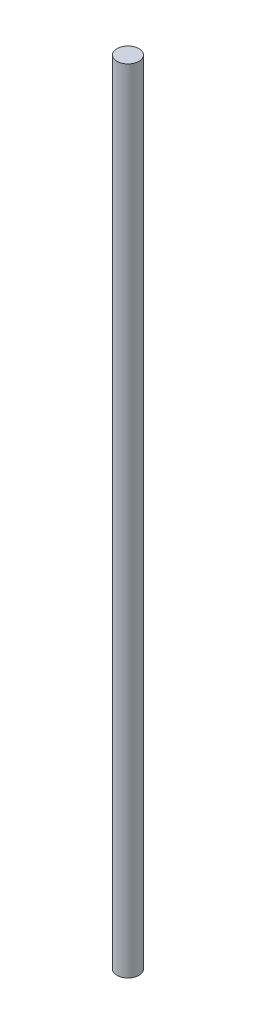
SolidWorks part; units mm, degrees
ref_plane "Front Plane" through (0, 0, 0) normal (0, 0, 1) x (1, 0, 0)
ref_plane "Top Plane" through (0, 0, 0) normal (0, 1, 0) x (1, 0, 0)
ref_plane "Right Plane" through (0, 0, 0) normal (1, 0, 0) x (0, 0, -1)
sketch "Sketch1" plane through (0, 0, 0) normal (0, 1, 0) x (1, 0, 0)
  circle A0 centre (0, 0) radius 3.175
  dimension "D1" = 6.35
extrude "Boss-Extrude1" add sketch "Sketch1" along normal blind 228.6 contours A0
